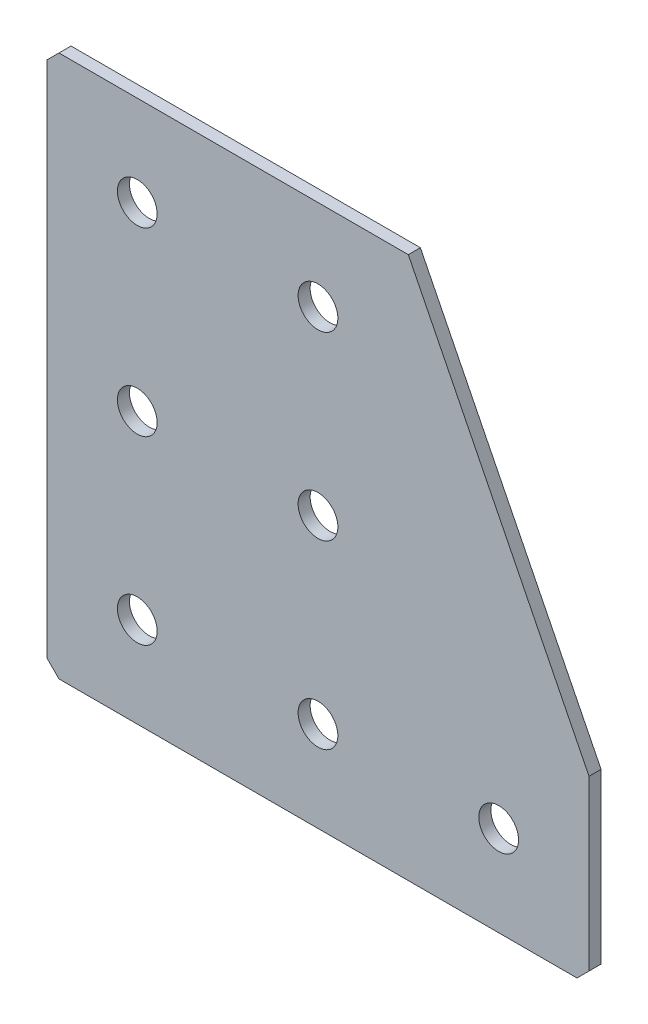
SolidWorks part; units mm, degrees
material "Простая углеродистая сталь"
ref_plane "Спереди(Плоскость XY)" through (0, 0, 0) normal (0, 0, 1) x (1, 0, 0)
ref_plane "Сверху(Плоскость XZ)" through (0, 0, 0) normal (0, 1, 0) x (1, 0, 0)
ref_plane "Справа(Плоскость ZY)" through (0, 0, 0) normal (1, 0, 0) x (0, 0, -1)
sketch "Эскиз1" plane through (0, 0, 0) normal (0, 0, -1) x (1, 0, 0)
  line L0 (0, 0) -> (0, 90)
  line L1 (0, 90) -> (90, 90)
  line L2 (90, 90) -> (90, 60)
  line L3 (90, 60) -> (60, 60) construction
  line L4 (60, 60) -> (60, 0) construction
  line L5 (60, 0) -> (0, 0)
  line L6 (90, 60) -> (60, 0)
  dimension "D1" = 90
  dimension "D2" = 30
  dimension "D3" = 60
extrude "Бобышка-Вытянуть1" add sketch "Эскиз1" along normal blind 2
hole_wizard "Отверстие с зазором M61" positions "Эскиз2" profile "Эскиз3" hole size "M6" standard "IS" end condition through all
sketch "Эскиз2" plane through (0, 0, -2) normal (0, 0, -1) x (1, 0, 0)
  line L0 (15, 0) -> (15, 90) construction
  line L1 (0, 0) -> (60, 0) construction
  line L2 (90, 90) -> (0, 90) construction
  line L3 (90, 75) -> (0, 75) construction
  line L4 (90, 60) -> (90, 90) construction
  line L5 (0, 90) -> (0, 0) construction
  point P0 (45, 75)
  point P2 (15, 75)
  point P4 (15, 45)
  point P6 (15, 15)
  point P21 (75, 75)
  point P24 (45, 45)
  point P26 (45, 15)
  dimension "D1" = 30
  dimension "D2" = 30
  dimension "D3" = 30
  dimension "D4" = 15
  dimension "D5" = 30
  dimension "D6" = 15
sketch "Эскиз3" plane through (45, -75, -2) normal (1, 0, 0) x (0, 1, 0)
  line L0 (0, 0) -> (0, 2)
  line L1 (0, 2) -> (3.3, 2)
  line L2 (3.3, 2) -> (3.3, 0)
  line L5 (3.3, 0) -> (0, 0)
  line L11 (0, -6.35) -> (0, 107.95) construction
  dimension "Диаметр сквозного отверстия" = 6.6
  dimension "Глубина сквозного отверстия" = 2
chamfer "Фаска1" distance 2 angle 45 3 edges at (0, 0, -1) (90, -90, -1) (0, -90, -1)
